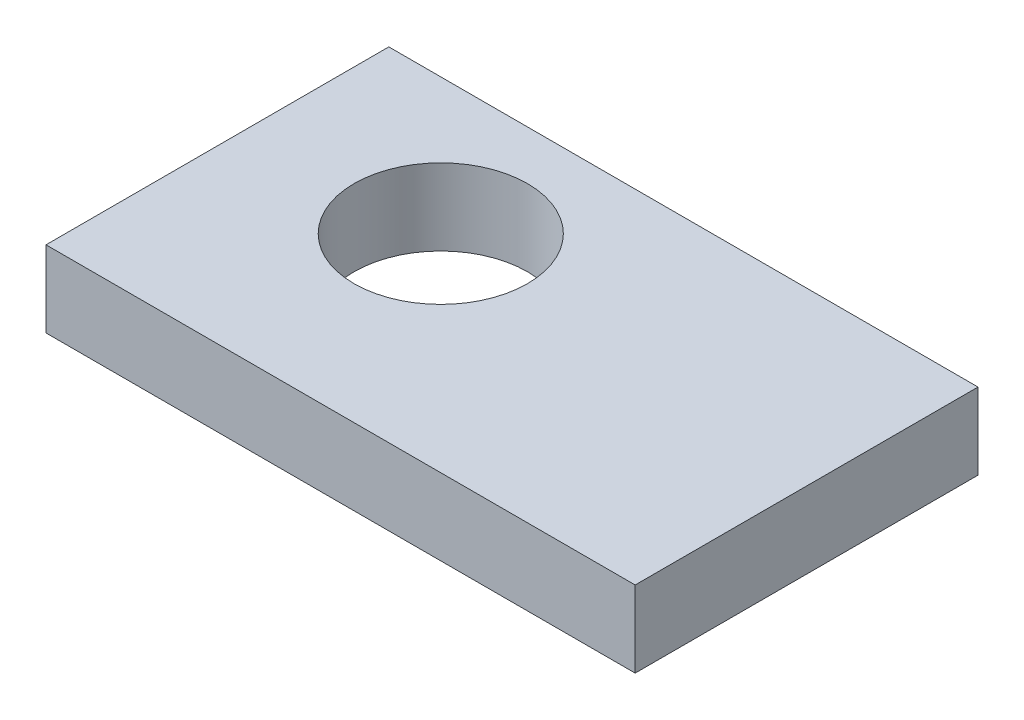
SolidWorks part; units mm, degrees
material "Rubber"
ref_plane "Front Plane" through (0, 0, 0) normal (0, 0, 1) x (1, 0, 0)
ref_plane "Top Plane" through (0, 0, 0) normal (0, 1, 0) x (1, 0, 0)
ref_plane "Right Plane" through (0, 0, 0) normal (1, 0, 0) x (0, 0, -1)
sketch "Sketch1" plane through (0, 0, 0) normal (0, 1, 0) x (1, 0, 0)
  line L1 (-55.2491, 27.5574) -> (21.9115, 27.5574)
  line L2 (-55.2491, 27.5574) -> (-55.2491, -17.341)
  line L3 (-55.2491, -17.341) -> (21.9115, -17.341)
  line L4 (21.9115, 27.5574) -> (21.9115, -17.341)
extrude "Boss-Extrude1" add sketch "Sketch1" along normal blind 10
sketch "Sketch2" plane through (0, 10, 0) normal (0, 1, 0) x (1, 0, 0)
  circle A0 centre (-30.6664, 9.7773) radius 11.3536
extrude "Cut-Extrude1" cut sketch "Sketch2" against normal blind 10
